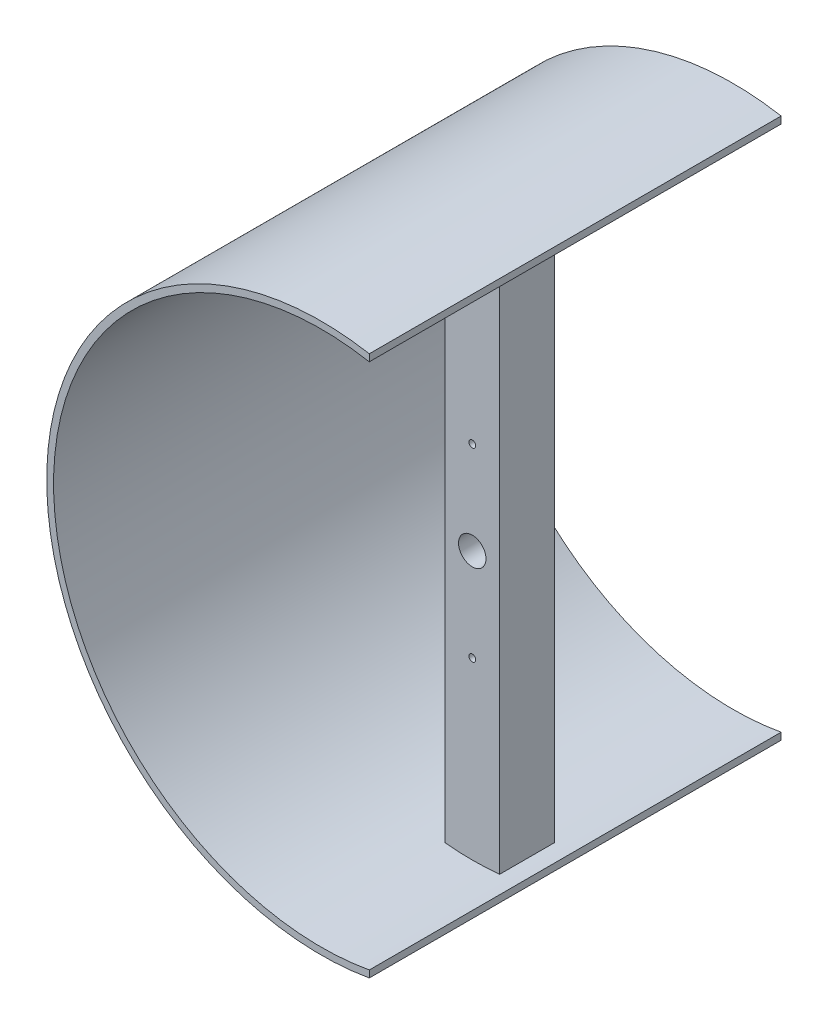
SolidWorks part; units mm, degrees
ref_plane "Plan de face" through (0, 0, 0) normal (0, 0, 1) x (1, 0, 0)
ref_plane "Plan de dessus" through (0, 0, 0) normal (0, 1, 0) x (1, 0, 0)
ref_plane "Plan de droite" through (0, 0, 0) normal (1, 0, 0) x (0, 0, -1)
sketch "Esquisse1" plane through (0, 0, 0) normal (0, 0, 1) x (1, 0, 0)
  line L1 (0, 0) -> (8, 0)
  line L2 (0, 0) -> (0, 79)
  line L3 (0, 79) -> (8, 79)
  line L4 (8, 0) -> (8, 79)
  dimension "D1" = 79
  dimension "D2" = 8
extrude "Boss.-Extru.1" add sketch "Esquisse1" along normal blind 60
sketch "Esquisse3" plane through (0, 0, 0) normal (0, 0, -1) x (-1, 0, 0)
  line L0 (-4, 79) -> (-4, 0) construction
  line L1 (-8, 79) -> (0, 79) construction
  line L2 (0, 0) -> (-8, 0) construction
  line L3 (0, 39.5) -> (-8, 39.5) construction
  line L4 (0, 79) -> (0, 0) construction
  line L5 (-8, 0) -> (-8, 79) construction
  circle A0 centre (-4, 39.5) radius 40
  circle A1 centre (-4, 39.5) radius 39
  dimension "D1" = 80
  dimension "D2" = 78
extrude "Boss.-Extru.2" add sketch "Esquisse3" against normal blind 60
sketch "Esquisse4" plane through (0, 0, 0) normal (0, 0, -1) x (-1, 0, 0)
  line L0 (-4, -0.5) -> (-4, 79.5) construction
  line L1 (-43.5151, 39.5) -> (32.2355, 39.5) construction
  circle A0 centre (-4, 39.5) radius 40 construction
  circle A5 centre (-4, 39.5) radius 39
  dimension "D1" = 78
extrude "Enlèv. mat.-Extru.3" cut sketch "Esquisse4" against normal blind 30
sketch "Esquisse5" plane through (0, 0, 30) normal (0, 0, -1) x (-1, 0, 0)
  line L0 (-4, 78.5) -> (-4, 0.5) construction
  line L1 (35, 39.5) -> (-43, 39.5) construction
  line L3 (-6, 53) -> (-6.9673, 39.942)
  line L5 (-6, 26) -> (-6.9673, 39.058)
  line L6 (-1.0327, 39.942) -> (-2, 53)
  line L7 (-2, 26) -> (-1.0327, 39.058)
  arc A0 (0, 78.2943) -> (-8, 78.2943) centre (-4, 39.5) ccw construction
  arc A1 (-8, 0.7057) -> (0, 0.7057) centre (-4, 39.5) ccw construction
  circle A2 centre (-4, 39.5) radius 39 construction
  arc A3 (-6.9673, 39.942) -> (-6.9673, 39.058) centre (-4, 39.5) ccw
  arc A4 (-2, 53) -> (-6, 53) centre (-4, 53) ccw
  arc A5 (-2, 26) -> (-6, 26) centre (-4, 26) cw
  arc A7 (-1.0327, 39.942) -> (-1.0327, 39.058) centre (-4, 39.5) cw
  dimension "D1" = 6
  dimension "D2" = 4
  dimension "D3" = 13.5
  dimension "D4" = 13.058
  dimension "D5" = 13.058
  dimension "D6" = 171.527
extrude "Enlèv. mat.-Extru.5" cut sketch "Esquisse5" against normal blind 1.5
sketch "Esquisse6" plane through (0, 0, 60) normal (0, 0, 1) x (1, 0, 0)
  line L0 (4, 79.5) -> (4, -0.5) construction
  line L1 (-35, 39.5) -> (43, 39.5) construction
  circle A0 centre (4, 39.5) radius 40 construction
  arc A1 (0, 78.2943) -> (0, 0.7057) centre (4, 39.5) ccw construction
  arc A2 (8, 0.7057) -> (8, 78.2943) centre (4, 39.5) ccw construction
  circle A3 centre (4, 39.5) radius 39
  dimension "D1" = 78
extrude "Enlèv. mat.-Extru.6" cut sketch "Esquisse6" against normal blind 22
sketch "Esquisse7" plane through (0, 0, 31.5) normal (0, 0, -1) x (-1, 0, 0)
  line L0 (-4, 55) -> (-4, 24) construction
  line L1 (-4, 24) -> (-43, 39.5) construction
  line L2 (-43, 39.5) -> (35, 39.5) construction
  arc A0 (-2, 53) -> (-6, 53) centre (-4, 53) ccw construction
  arc A1 (-6, 26) -> (-2, 26) centre (-4, 26) ccw construction
  circle A2 centre (-4, 39.5) radius 39 construction
  circle A3 centre (-4, 39.5) radius 2
  dimension "D1" = 4
extrude "Enlèv. mat.-Extru.7" cut sketch "Esquisse7" against normal blind 6.5
sketch "Esquisse8" plane through (0, 0, 31.5) normal (0, 0, -1) x (-1, 0, 0)
  line L0 (-4, 55) -> (-4, 24) construction
  line L1 (-43, 39.5) -> (35, 39.5) construction
  arc A0 (-2, 53) -> (-6, 53) centre (-4, 53) ccw construction
  arc A1 (-6, 26) -> (-2, 26) centre (-4, 26) ccw construction
  circle A2 centre (-4, 39.5) radius 39 construction
sketch "Esquisse9" plane through (0, 0, 31.5) normal (0, 0, -1) x (-1, 0, 0)
  line L0 (-23.944, 39.5) -> (17.5488, 39.5) construction
  line L1 (-43, 39.5) -> (35, 39.5) construction
  circle A0 centre (-4, 53) radius 0.5
  circle A1 centre (-4, 26) radius 0.5
  dimension "D1" = 1
  dimension "D2" = 2
extrude "Enlèv. mat.-Extru.8" cut sketch "Esquisse9" against normal through all
sketch "Esquisse10" plane through (0, 0, 0) normal (0, 0, -1) x (-1, 0, 0)
  line L0 (-4, -5.342) -> (-4, 83.9627) construction
sketch "Esquisse11" plane through (0, 0, 0) normal (0, 0, 1) x (1, 0, 0)
  line L4 (4, -5.342) -> (4, 83.9627) construction
  line L5 (43, 39.5) -> (-35, 39.5) construction
  line L7 (51, 80.5) -> (11, 80.5)
  line L8 (51, 80.5) -> (51, -1.5)
  line L9 (51, -1.5) -> (11, -1.5)
  line L10 (11, 80.5) -> (11, -1.5)
  point P13 (11, 39.5)
  dimension "D3" = 0
  dimension "D4" = 82
  dimension "D5" = 7
  dimension "D6" = 40
extrude "Enlèv. mat.-Extru.10" cut sketch "Esquisse11" along normal up to next
